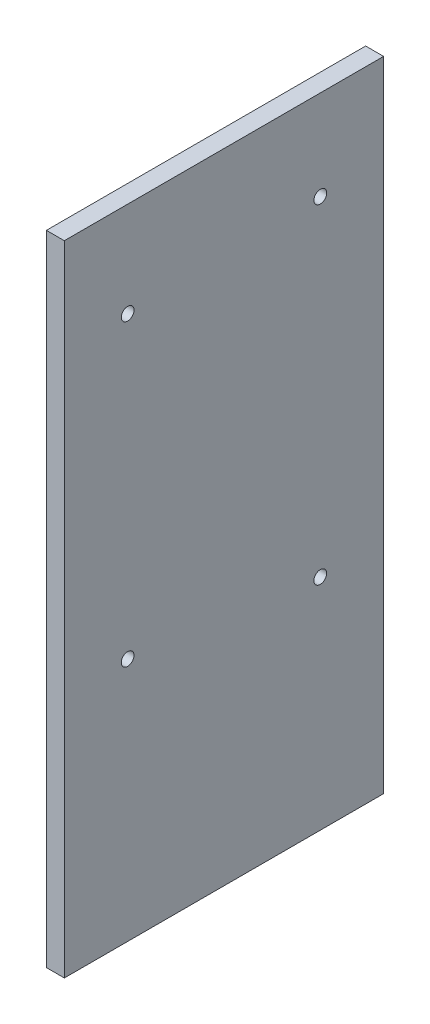
SolidWorks part; units mm, degrees
ref_plane "Front Plane" through (0, 0, 0) normal (0, 0, 1) x (1, 0, 0)
ref_plane "Top Plane" through (0, 0, 0) normal (0, 1, 0) x (1, 0, 0)
ref_plane "Right Plane" through (0, 0, 0) normal (1, 0, 0) x (0, 0, -1)
sketch "Sketch1" plane through (0, 0, 0) normal (1, 0, 0) x (0, 0, -1)
  line L1 (-40, -80) -> (40, -80)
  line L2 (-40, -80) -> (-40, 80)
  line L3 (-40, 80) -> (40, 80)
  line L4 (40, -80) -> (40, 80)
  line L5 (-40, -80) -> (40, 80) construction
  line L6 (-40, 80) -> (40, -80) construction
  point P0 (0, 0)
  dimension "D1" = 160
  dimension "D2" = 80
extrude "Boss-Extrude1" add sketch "Sketch1" along normal blind 4.5
sketch "Sketch2" plane through (0, 0, 0) normal (-1, 0, 0) x (0, 0, 1)
  line L0 (-40, -80) -> (-40, 80) construction
  line L2 (-40, 80) -> (40, 80) construction
  circle A0 centre (-24.14, 57.5) radius 1.6
  circle A1 centre (24.14, 56.23) radius 1.6
  circle A2 centre (24.14, -18.7) radius 1.6
  circle A3 centre (-24.12, -25.05) radius 1.6
  point P12 (0, 0)
  dimension "D1" = 74.93
  dimension "D2" = 15.86
  dimension "D3" = 22.5
  dimension "D4" = 48.26
  dimension "D5" = 82.55
  dimension "D6" = 23.77
extrude "Cut-Extrude1" cut sketch "Sketch2" against normal blind 4.5
